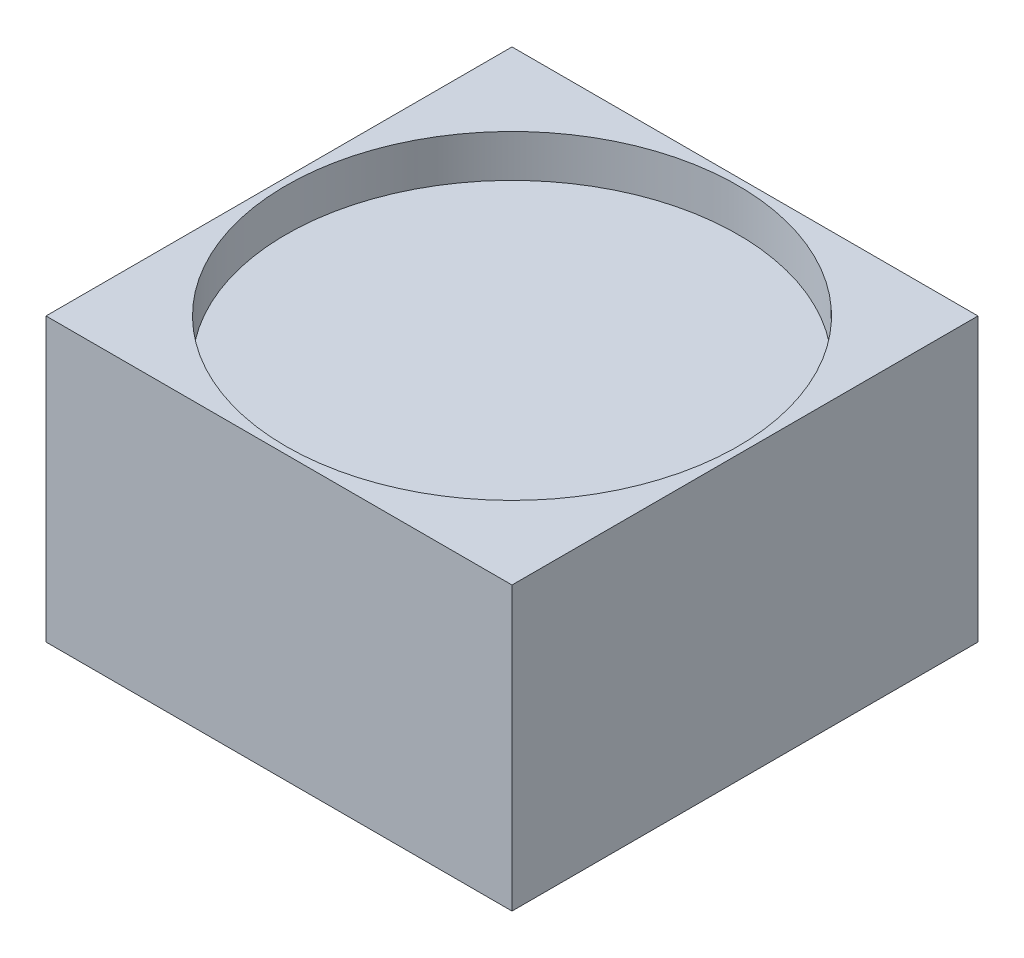
SolidWorks part; units mm, degrees
ref_plane "Front Plane" through (0, 0, 0) normal (0, 0, 1) x (1, 0, 0)
ref_plane "Top Plane" through (0, 0, 0) normal (0, 1, 0) x (1, 0, 0)
ref_plane "Right Plane" through (0, 0, 0) normal (1, 0, 0) x (0, 0, -1)
sketch "Sketch1" plane through (0, 0, 0) normal (0, 1, 0) x (1, 0, 0)
  line L1 (-16.5, -16.5) -> (16.5, -16.5)
  line L2 (-16.5, -16.5) -> (-16.5, 16.5)
  line L3 (-16.5, 16.5) -> (16.5, 16.5)
  line L4 (16.5, -16.5) -> (16.5, 16.5)
  line L5 (-16.5, -16.5) -> (16.5, 16.5) construction
  line L6 (-16.5, 16.5) -> (16.5, -16.5) construction
  point P0 (0, 0)
  dimension "D1" = 33
  dimension "D2" = 33
extrude "Boss-Extrude1" add sketch "Sketch1" along normal blind 20
sketch "Sketch2" plane through (0, 20, 0) normal (0, 1, 0) x (1, 0, 0)
  circle A0 centre (0, 0) radius 16
  dimension "D1" = 32
extrude "Cut-Extrude1" cut sketch "Sketch2" against normal blind 3
sketch "Sketch3" plane through (0, 0, 0) normal (0, -1, 0) x (1, 0, 0)
  circle A0 centre (0, 0) radius 1
  dimension "D1" = 2
extrude "Cut-Extrude2" cut sketch "Sketch3" against normal blind 2
fillet "Fillet1" radius 1 1 edges at (0, 2, -1)
